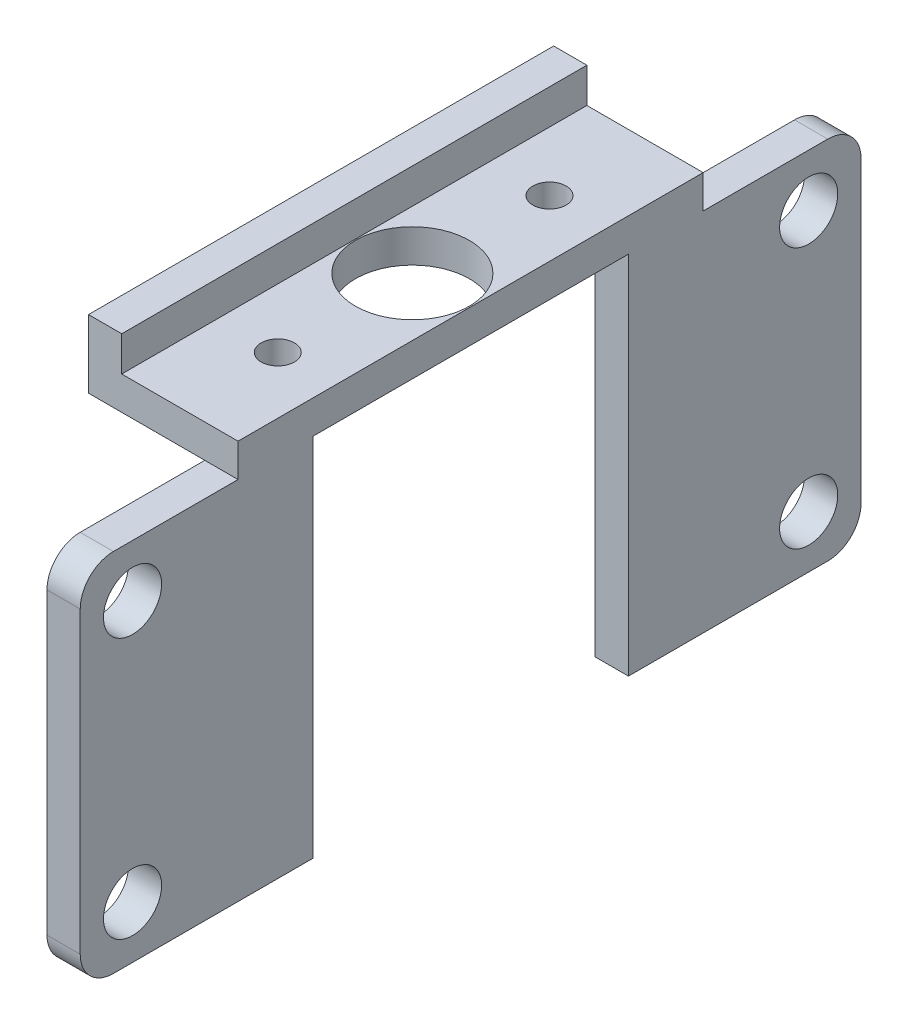
SolidWorks part; units mm, degrees
ref_plane "Front Plane" through (0, 0, 0) normal (0, 0, 1) x (1, 0, 0)
ref_plane "Top Plane" through (0, 0, 0) normal (0, 1, 0) x (1, 0, 0)
ref_plane "Right Plane" through (0, 0, 0) normal (1, 0, 0) x (0, 0, -1)
sketch "Sketch3" plane through (0, 0, 0) normal (0, 0, 1) x (1, 0, 0)
  line L0 (-16.9532, 6.6875) -> (-14.9532, 6.6875)
  line L1 (-14.9532, 6.6875) -> (-14.9532, 4.5875)
  line L2 (-14.9532, 4.5875) -> (-7.9532, 4.5875)
  line L3 (-7.9532, 4.5875) -> (-7.9532, -19.4125)
  line L4 (-7.9532, -19.4125) -> (-9.9532, -19.4125)
  line L5 (-9.9532, -19.4125) -> (-9.9532, 2.5875)
  line L6 (-9.9532, 2.5875) -> (-16.9532, 2.5875)
  line L7 (-16.9532, 2.5875) -> (-16.9532, 6.6875)
  dimension "D1" = 2
  dimension "D2" = 4.1
  dimension "D3" = 7
  dimension "D4" = 2
  dimension "D5" = 24
  dimension "D6" = 2
extrude "Boss-Extrude3" add sketch "Sketch3" along normal blind 28
sketch "Sketch4" plane through (0, 4.5875, 0) normal (0, 1, 0) x (1, 0, 0)
  line L0 (-7.9532, -28) -> (-7.9532, 0) construction
  line L1 (-7.9532, 0) -> (-14.9532, 0) construction
  circle A0 centre (-11.4584, -14) radius 3.43
  circle A1 centre (-11.3832, -5.822) radius 1
  circle A2 centre (-11.3832, -22.1777) radius 1
  dimension "D1" = 6.86
  dimension "D2" = 2
  dimension "D3" = 3.43
  dimension "D4" = 2
  dimension "D5" = 3.43
  dimension "D6" = 8.178
  dimension "D7" = 8.178
  dimension "D8" = 14
extrude "Cut-Extrude1" cut sketch "Sketch4" against normal blind 2
sketch "Sketch6" plane through (0, 0, 0) normal (0, 0, -1) x (-1, 0, 0)
  line L1 (7.9532, -19.4125) -> (9.9532, -19.4125)
  line L2 (7.9532, -19.4125) -> (7.9532, 2.5875)
  line L3 (7.9532, 2.5875) -> (9.9532, 2.5875)
  line L4 (9.9532, -19.4125) -> (9.9532, 2.5875)
extrude "Boss-Extrude4" add sketch "Sketch6" along normal blind 9.5
sketch "Sketch7" plane through (0, 0, 28) normal (0, 0, 1) x (1, 0, 0)
  line L1 (-7.9532, -19.4125) -> (-9.9532, -19.4125)
  line L2 (-7.9532, -19.4125) -> (-7.9532, 2.5875)
  line L3 (-7.9532, 2.5875) -> (-9.9532, 2.5875)
  line L4 (-9.9532, -19.4125) -> (-9.9532, 2.5875)
extrude "Boss-Extrude5" add sketch "Sketch7" along normal blind 9.5
fillet "Fillet1" radius 2 1 edges at (-8.9532, 2.5875, 37.5)
fillet "Fillet2" radius 2 1 edges at (-8.9532, 2.5875, -9.5)
fillet "Fillet3" radius 2 2 edges at (-8.9532, -19.4125, -9.5) (-8.9532, -19.4125, 37.5)
sketch "Sketch8" plane through (-9.9532, 0, 0) normal (-1, 0, 0) x (0, 0, 1)
  circle A0 centre (34.35, -0.5625) radius 1.75
  circle A1 centre (-6.35, -0.5625) radius 1.75
  circle A2 centre (-6.35, -16.2625) radius 1.75
  circle A3 centre (34.35, -16.2625) radius 1.75
  dimension "D1" = 3.5
  dimension "D2" = 3.5
  dimension "D3" = 3.5
  dimension "D4" = 3.5
extrude "Cut-Extrude2" cut sketch "Sketch8" against normal up to next
sketch "Sketch9" plane through (-7.9532, 0, 0) normal (1, 0, 0) x (0, 0, -1)
  line L0 (-35.5, -19.4125) -> (7.5, -19.4125) construction
  line L1 (-23.5, -19.4125) -> (-4.5, -19.4125)
  line L2 (-23.5, -19.4125) -> (-23.5, 2.5875)
  line L3 (-23.5, 2.5875) -> (-4.5, 2.5875)
  line L4 (-4.5, -19.4125) -> (-4.5, 2.5875)
  line L5 (7.5, 2.5875) -> (0, 2.5875) construction
  line L6 (9.5, 0.5875) -> (9.5, -17.4125) construction
  line L7 (-37.5, -17.4125) -> (-37.5, 0.5875) construction
  dimension "D1" = 14
  dimension "D2" = 14
extrude "Cut-Extrude3" cut sketch "Sketch9" against normal up to next
